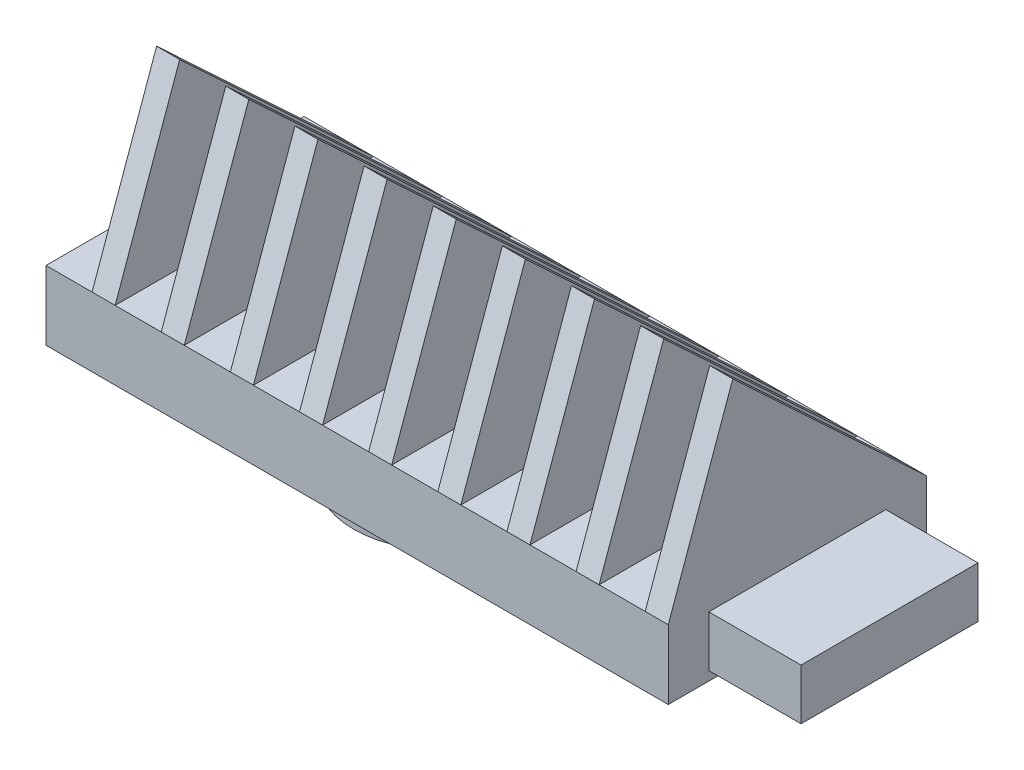
SolidWorks part; units mm, degrees
ref_plane "Front Plane" through (0, 0, 0) normal (0, 0, 1) x (1, 0, 0)
ref_plane "Top Plane" through (0, 0, 0) normal (0, 1, 0) x (1, 0, 0)
ref_plane "Right Plane" through (0, 0, 0) normal (1, 0, 0) x (0, 0, -1)
sketch "Sketch1" plane through (0, 0, 0) normal (0, 1, 0) x (1, 0, 0)
  line L1 (0, 0) -> (-211.1375, 0)
  line L2 (0, 0) -> (0, 35.56)
  line L3 (0, 35.56) -> (-211.1375, 35.56)
  line L4 (-211.1375, 0) -> (-211.1375, 35.56)
  dimension "D1" = 211.1375
extrude "Boss-Extrude1" add sketch "Sketch1" along normal blind 9.525
sketch "Sketch2" plane through (0, 9.525, 0) normal (0, 1, 0) x (1, 0, 0)
  line L0 (-211.1375, 0) -> (0, 0) construction
  line L1 (-211.1375, 35.56) -> (-207.8355, 35.56)
  line L2 (-211.1375, 35.56) -> (-211.1375, 0)
  line L3 (-211.1375, 0) -> (-207.8355, 0)
  line L4 (-207.8355, 35.56) -> (-207.8355, 0)
  dimension "D1" = 3.302
ref_plane "Plane1" through (0, 34.417, 0) normal (0, 1, 0) x (1, 0, 0)
sketch "Sketch5" plane through (0, 34.417, 0) normal (0, 1, 0) x (1, 0, 0)
  line L2 (-213.741, 8.89) -> (-207.8355, 8.89)
  line L3 (-207.8355, 35.56) -> (-207.8355, 0) construction
sketch "Sketch6" plane through (0, 0, 0) normal (0, -1, 0) x (-1, 0, 0)
  line L5 (0, 0) -> (0, 35.56) construction
  line L6 (211.1375, 35.56) -> (211.1375, 0) construction
  circle A0 centre (105.5687, 17.78) radius 12.192
  circle A1 centre (36.7982, 17.78) radius 12.192
  circle A2 centre (174.3392, 17.78) radius 12.192
  dimension "D1" = 36.7982
  dimension "D2" = 24.384
  dimension "D3" = 68.7705
  dimension "D4" = 24.384
  dimension "D5" = 24.384
  dimension "D6" = 36.7983
  dimension "D7" = 68.7705
extrude "Boss-Extrude4" add sketch "Sketch6" along normal blind 6.35
sketch3d "3DSketch1"
  line L0 (-207.8355, 9.525, -35.56) -> (-207.8355, 9.525, 0)
  line L1 (-207.8355, 9.525, 0) -> (-207.8355, 34.417, -8.89)
  line L2 (-207.8355, 34.417, -8.89) -> (-207.8355, 9.525, -35.56)
ref_plane "Plane2" through (-204.7875, 0, 0) normal (-1, 0, 0) x (0, 0, 1)
sketch "Sketch9" plane through (-204.7875, 0, 0) normal (-1, 0, 0) x (0, 0, 1)
  line L0 (-35.56, 9.525) -> (0, 9.525)
  line L1 (0, 9.525) -> (-8.89, 34.417)
  line L2 (-8.89, 34.417) -> (-35.56, 9.525)
extrude "Boss-Extrude5" add sketch "Sketch9" against normal blind 3.175
pattern_linear "LPattern1" count 22 spacing 9.525 along (1, 0, 0) of "Boss-Extrude5"
sketch "Sketch10" plane through (0, 0, 0) normal (1, 0, 0) x (0, 0, -1)
  line L1 (-12.2101, -28.9523) -> (47.7701, -28.9523)
  line L2 (-12.2101, -28.9523) -> (-12.2101, 38.3196)
  line L3 (-12.2101, 38.3196) -> (47.7701, 38.3196)
  line L4 (47.7701, -28.9523) -> (47.7701, 38.3196)
  line L5 (-12.2101, -28.9523) -> (47.7701, 38.3196) construction
  line L6 (-12.2101, 38.3196) -> (47.7701, -28.9523) construction
  point P0 (17.78, 4.6836)
extrude "Cut-Extrude1" cut sketch "Sketch10" against normal up to surface (125.4125 mm away) up to face at (-125.4125, 17.8223, -14.8167)
sketch "Sketch11" plane through (-125.4125, 0, 0) normal (1, 0, 0) x (0, 0, -1)
  line L4 (5.588, 1.2573) -> (29.972, 1.2573)
  line L5 (5.588, 1.2573) -> (5.588, 8.2677)
  line L6 (5.588, 8.2677) -> (29.972, 8.2677)
  line L7 (29.972, 1.2573) -> (29.972, 8.2677)
  line L8 (5.588, 1.2573) -> (29.972, 8.2677) construction
  line L9 (5.588, 8.2677) -> (29.972, 1.2573) construction
  point P6 (17.78, 4.7625)
  dimension "D1" = 24.384
  dimension "D2" = 7.0104
extrude "Boss-Extrude6" add sketch "Sketch11" along normal blind 12.7
